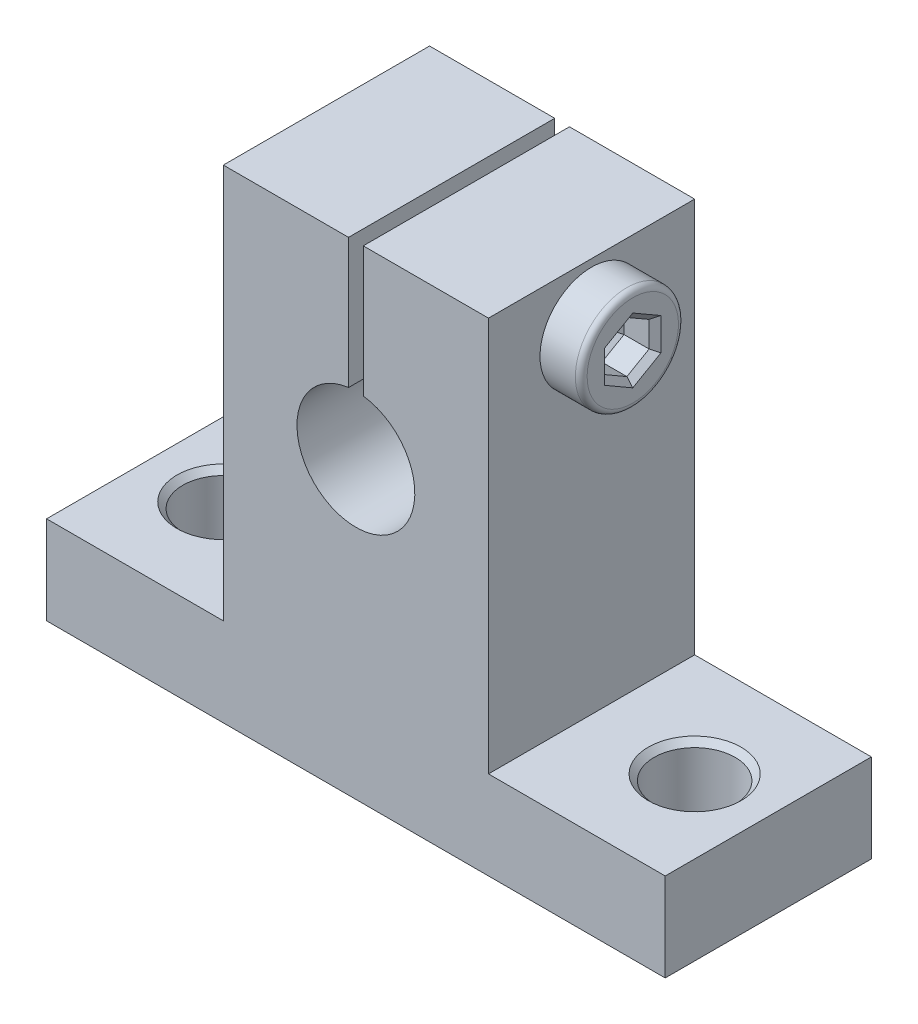
SolidWorks part; units mm, degrees
material "Lega 6061"
ref_plane "Front" through (0, 0, 0) normal (0, 0, 1) x (1, 0, 0)
ref_plane "Top" through (0, 0, 0) normal (0, 1, 0) x (1, 0, 0)
ref_plane "Right" through (0, 0, 0) normal (1, 0, 0) x (0, 0, -1)
sketch "Sketch1" plane through (0, 0, 0) normal (0, 0, 1) x (1, 0, 0)
  line L0 (0, 32.8) -> (0, -11.1975) construction
  line L1 (-21, 0) -> (21, 0)
  line L2 (-21, 0) -> (-21, 6)
  line L3 (-21, 6) -> (-9, 6)
  line L4 (21, 0) -> (21, 6)
  line L5 (9, 6) -> (21, 6)
  line L7 (-9, 6) -> (-9, 32.8)
  line L8 (-9, 32.8) -> (9, 32.8)
  line L9 (9, 6) -> (9, 32.8)
  circle A0 centre (0, 20) radius 4
  dimension "D4" = 8
  dimension "D1" = 6
  dimension "D2" = 42
  dimension "D3" = 18
  dimension "D5" = 32.8
  dimension "20" = 20
extrude "Boss-Extrude1" add sketch "Sketch1" along normal blind 14
sketch "Sketch2" plane through (9, 0, 0) normal (1, 0, 0) x (0, 0, -1)
  line L0 (-14, 32.8) -> (0, 32.8) construction
  line L1 (-7, 32.8) -> (-7, 14.0812) construction
  circle A0 centre (-7, 28.8) radius 2
  dimension "D1" = 4
  dimension "D2" = 4
sketch "Sketch3" plane through (0, 0, 14) normal (0, 0, 1) x (1, 0, 0)
  line L0 (9, 32.8) -> (-9, 32.8) construction
  line L1 (-0.5, 32.8) -> (0.5, 32.8)
  line L2 (-0.5, 32.8) -> (-0.5, 21.0098)
  line L3 (-0.5, 21.0098) -> (0.5, 21.0098)
  line L4 (0.5, 32.8) -> (0.5, 21.0098)
  line L5 (0, 32.8) -> (0, 12.111) construction
  dimension "D1" = 1
extrude "Cut-Extrude1" cut sketch "Sketch3" against normal blind 19 contours L4 L3 L2 L1
extrude "Cut-Extrude3" cut sketch "Sketch2" against normal blind 31 contours A0
sketch "Sketch5" plane through (0, 6, 0) normal (0, 1, 0) x (1, 0, 0)
  line L0 (0, 7.6779) -> (0, -23.3122) construction
  line L1 (21, -7) -> (-21, -7) construction
  line L4 (21, -14) -> (21, 0) construction
  line L5 (-21, -14) -> (-21, 0) construction
  circle A0 centre (16, -7) radius 2.75
  circle A1 centre (-16, -7) radius 2.75
  dimension "D1" = 32
  dimension "D2" = 5.5
extrude "Cut-Extrude5" cut sketch "Sketch5" against normal blind 22
ref_plane "Piano1" through (0, 0, 7) normal (0, 0, 1) x (1, 0, 0)
sketch "Schizzo1" plane through (0, 0, 7) normal (0, 0, 1) x (1, 0, 0)
  line L0 (-22.7047, 28.8) -> (19.8969, 28.8) construction
  line L4 (11.8, 28.8) -> (-11, 28.8)
  line L5 (-11, 28.8) -> (-11, 30.4)
  line L6 (-10.6, 30.8) -> (9, 30.8)
  line L12 (9, 32.8) -> (0.5, 32.8) construction
  line L13 (-11, 30.4) -> (-10.6, 30.8)
  line L14 (9, 30.8) -> (9, 32.3)
  line L15 (9, 32.3) -> (11.8, 32.3)
  line L16 (11.8, 32.3) -> (11.8, 28.8)
  line L17 (9, 6) -> (9, 32.8) construction
  point P7 (-11, 30.8)
  dimension "D1" = 22.8
  dimension "D2" = 3.5
  dimension "D3" = 2.8
  dimension "D6" = 2
  dimension "D7" = 2
revolve "Rivoluzione1" add sketch "Schizzo1" angle 360 about L0
cosmetic thread "Filettatura cosmetica1" parameters "D2"=3.22
sketch "Schizzo2" plane through (11.8, 0, 0) normal (1, 0, 0) x (0, 0, -1)
  line L1 (-7, 30.5383) -> (-8.5054, 29.6691)
  line L2 (-8.5054, 29.6691) -> (-8.5054, 27.9309)
  line L3 (-8.5054, 27.9309) -> (-7, 27.0617)
  line L4 (-7, 27.0617) -> (-5.4946, 27.9309)
  line L5 (-5.4946, 27.9309) -> (-5.4946, 29.6691)
  line L6 (-5.4946, 29.6691) -> (-7, 30.5383)
  circle A0 centre (-7, 28.8) radius 1.5 construction
  circle A1 centre (-7, 28.8) radius 1.5054 construction
  dimension "D1" = 3
  dimension "D2" = 1.5054
extrude "Taglio-Estrusione1" cut sketch "Schizzo2" against normal blind 2.5
chamfer "Smusso1" distance 0.4 angle 45 12 edges at (11.8, 28.8, 8.5054) (11.8, 27.4963, 7.7527) (11.8, 27.4963, 6.2473) (11.8, 28.8, 5.4946) (11.8, 30.1037, 6.2473) (11.8, 30.1037, 7.7527) (9.3, 28.8, 5.4946) (9.3, 27.4963, 6.2473) (9.3, 27.4963, 7.7527) (9.3, 28.8, 8.5054) (9.3, 30.1037, 7.7527) (9.3, 30.1037, 6.2473)
fillet "Raccordo1" radius 0.4 1 edges at (11.8, 25.3, 7)
chamfer "Smusso2" distance 0.4 angle 45 2 edges at (13.25, 6, 7) (-13.25, 6, 7)
